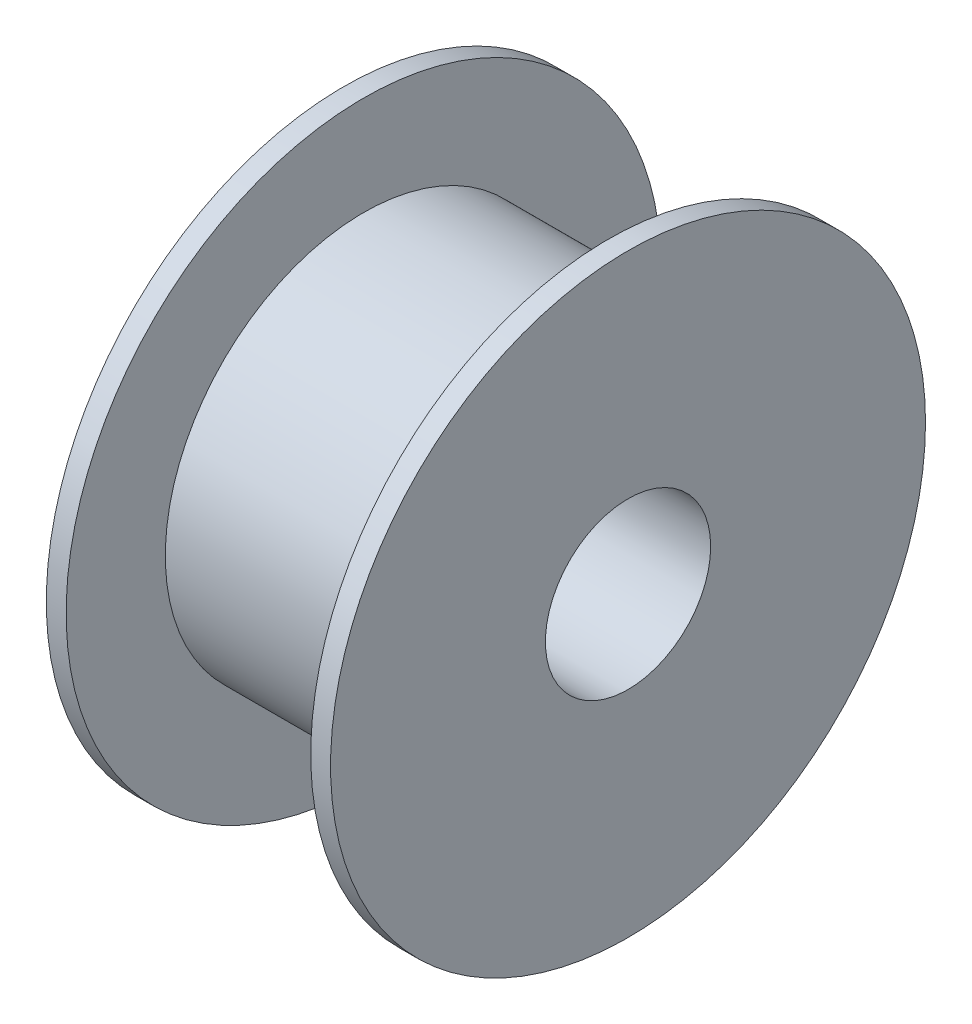
SolidWorks part; units mm, degrees
ref_plane "Front Plane" through (0, 0, 0) normal (0, 0, 1) x (1, 0, 0)
ref_plane "Top Plane" through (0, 0, 0) normal (0, 1, 0) x (1, 0, 0)
ref_plane "Right Plane" through (0, 0, 0) normal (1, 0, 0) x (0, 0, -1)
sketch "Sketch1" plane through (0, 0, 0) normal (0, 0, 1) x (1, 0, 0)
  line L0 (-0.6, 2.5) -> (8, 2.5)
  line L1 (8, 2.5) -> (8, 9)
  line L2 (8, 9) -> (7.4, 9)
  line L3 (7.4, 9) -> (7.4, 6)
  line L4 (7.4, 6) -> (0, 6)
  line L5 (0, 6) -> (0, 9)
  line L6 (0, 9) -> (-0.6, 9)
  line L7 (-0.6, 9) -> (-0.6, 2.5)
  line L8 (-0.6, 0) -> (8, 0) construction
revolve "Revolve1" add sketch "Sketch1" angle 360 about L8
